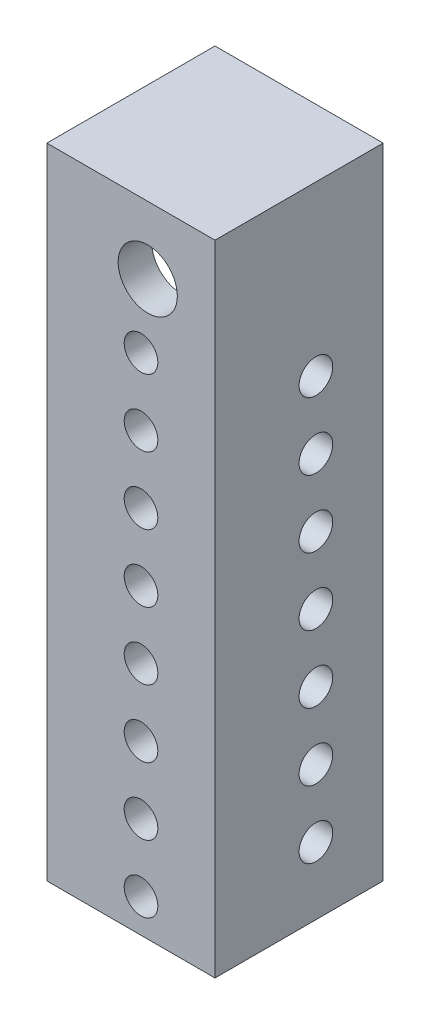
SolidWorks part; units mm, degrees
material "PET"
ref_plane "Front Plane" through (0, 0, 0) normal (0, 0, 1) x (1, 0, 0)
ref_plane "Top Plane" through (0, 0, 0) normal (0, 1, 0) x (1, 0, 0)
ref_plane "Right Plane" through (0, 0, 0) normal (1, 0, 0) x (0, 0, -1)
sketch "Sketch2" plane through (0, 0, 0) normal (0, 1, 0) x (1, 0, 0)
  line L1 (-41.3514, 38.3779) -> (22.1486, 38.3779)
  line L2 (-41.3514, 38.3779) -> (-41.3514, -25.1221)
  line L3 (-41.3514, -25.1221) -> (22.1486, -25.1221)
  line L4 (22.1486, 38.3779) -> (22.1486, -25.1221)
  dimension "D1" = 63.5
  dimension "D2" = 63.5
extrude "Boss-Extrude1" add sketch "Sketch2" along normal blind 241.3
ref_plane "Plane1" through (0, 116.078, 0) normal (0, 1, 0) x (1, 0, 0)
sketch "Sketch4" plane through (0, 116.078, 0) normal (0, 1, 0) x (1, 0, 0)
  line L0 (22.1486, -25.1221) -> (22.1486, 38.3779) construction
  line L1 (-41.3514, 38.3779) -> (9.4486, 38.3779)
  line L2 (-41.3514, 38.3779) -> (-41.3514, -12.4221)
  line L3 (-41.3514, -12.4221) -> (9.4486, -12.4221)
  line L4 (9.4486, 38.3779) -> (9.4486, -12.4221)
  line L5 (-41.3514, -25.1221) -> (22.1486, -25.1221) construction
  dimension "D1" = 12.7
  dimension "D2" = 12.7
extrude "Cut-Extrude1" cut sketch "Sketch4" along normal mid plane 190.5
sketch "Sketch5" plane through (0, 0, 25.1221) normal (0, 0, 1) x (1, 0, 0)
  line L1 (-41.3514, 0) -> (22.1486, 0) construction
  line L3 (-41.3514, 241.3) -> (-41.3514, 0) construction
  circle A4 centre (-5.7914, 12.7) radius 6.35
  circle A5 centre (-5.7914, 38.1) radius 6.35
  circle A6 centre (-5.7914, 63.5) radius 6.35
  circle A7 centre (-5.7914, 88.9) radius 6.35
  circle A8 centre (-5.7914, 114.3) radius 6.35
  circle A11 centre (-5.7914, 139.7) radius 6.35
  circle A12 centre (-5.7914, 165.1) radius 6.35
  circle A13 centre (-5.7914, 190.5) radius 6.35
  dimension "D1" = 35.56
  dimension "D4" = 12.7
  dimension "D3" = 12.7
  dimension "D2" = 8
extrude "Cut-Extrude2" cut sketch "Sketch5" against normal through all
sketch "Sketch6" plane through (22.1486, 0, 0) normal (1, 0, 0) x (0, 0, -1)
  line L0 (-25.1221, 0) -> (38.3779, 0) construction
  line L1 (38.3779, 241.3) -> (38.3779, 0) construction
  circle A4 centre (12.9779, 25.4) radius 6.35
  circle A5 centre (12.9779, 50.8) radius 6.35
  circle A6 centre (12.9779, 76.2) radius 6.35
  circle A7 centre (12.9779, 101.6) radius 6.35
  circle A8 centre (12.9779, 127) radius 6.35
  circle A9 centre (12.9779, 152.4) radius 6.35
  circle A10 centre (12.9779, 177.8) radius 6.35
  dimension "D1" = 25.4
  dimension "D4" = 12.7
  dimension "D2" = 25.4
  dimension "D3" = 7
extrude "Cut-Extrude3" cut sketch "Sketch6" against normal blind 12.7
sketch "Sketch7" plane through (0, 20.828, 0) normal (0, 1, 0) x (1, 0, 0)
  line L0 (22.1486, -25.1221) -> (22.1486, 38.3779) construction
  line L1 (-41.3514, 38.3779) -> (9.4486, 38.3779)
  line L2 (-41.3514, 38.3779) -> (-41.3514, -12.4221)
  line L3 (-41.3514, -12.4221) -> (-3.2514, -12.4221)
  line L4 (9.4486, 38.3779) -> (9.4486, 0.2779)
  line L5 (-41.3514, -25.1221) -> (22.1486, -25.1221) construction
  line L6 (9.4486, 0.2779) -> (9.4486, -12.4221)
  line L7 (9.4486, -12.4221) -> (-3.2514, -12.4221)
  dimension "D1" = 12.7
  dimension "D2" = 12.7
extrude "Cut-Extrude4" cut sketch "Sketch7" against normal through all
ref_plane "Plane2" through (0, 228.6, 0) normal (0, 1, 0) x (1, 0, 0)
sketch "Sketch42" plane through (0, 211.328, 0) normal (0, -1, 0) x (1, 0, 0)
  line L0 (-3.2514, 12.4221) -> (9.4486, 12.4221)
  line L1 (-41.3514, 12.4221) -> (-3.2514, 12.4221)
  line L2 (-41.3514, 12.4221) -> (-41.3514, -38.3779)
  line L3 (-41.3514, -38.3779) -> (9.4486, -38.3779)
  line L4 (9.4486, -0.2779) -> (9.4486, -38.3779)
  line L5 (9.4486, 12.4221) -> (9.4486, -0.2779)
extrude "Cut-Extrude8" cut sketch "Sketch42" against normal up to surface (17.272 mm away)
sketch "Sketch43" plane through (0, 228.6, 0) normal (0, 1, 0) x (1, 0, 0)
  line L0 (-41.3514, 38.3779) -> (-41.3514, -25.1221) construction
  line L1 (-10.8714, 33.5519) -> (-0.7114, 33.5519)
  line L2 (-10.8714, 33.5519) -> (-10.8714, 24.6619)
  line L3 (-10.8714, 24.6619) -> (-0.7114, 24.6619)
  line L4 (-0.7114, 33.5519) -> (-0.7114, 24.6619)
  line L5 (-10.8714, 16.7879) -> (-0.7114, 16.7879)
  line L6 (-10.8714, 16.7879) -> (-10.8714, 7.8979)
  line L7 (-10.8714, 7.8979) -> (-0.7114, 7.8979)
  line L8 (-0.7114, 16.7879) -> (-0.7114, 7.8979)
  line L9 (-41.3514, -25.1221) -> (22.1486, -25.1221) construction
  point P10 (0, 0)
  point P11 (11.8683, 18.5659)
  point P14 (0, 0)
  point P15 (0, 0)
  point P16 (0, 0)
  dimension "D1" = 33.02
  dimension "D2" = 7.874
  dimension "D3" = 8.89
  dimension "D4" = 10.16
  dimension "D6" = 30.48
extrude "Boss-Extrude4" add sketch "Sketch43" against normal blind 10.16
sketch "Sketch46" plane through (0, 0, -33.5519) normal (0, 0, -1) x (-1, 0, 0)
  line L0 (0.7114, 218.44) -> (10.8714, 218.44) construction
  line L1 (10.8714, 218.44) -> (10.8714, 228.6) construction
  circle A0 centre (5.7914, 223.52) radius 2.032
  dimension "D1" = 5.08
  dimension "D2" = 5.08
extrude "Cut-Extrude10" cut sketch "Sketch46" against normal up to surface (58.674 mm away) up to face at (0.5586, 190.5, 25.1221)
fillet "Fillet6" radius 3.81 4 edges at (-0.7114, 218.44, -12.3429) (-10.8714, 218.44, -12.3429) (-0.7114, 218.44, -29.1069) (-10.8714, 218.44, -29.1069)
sketch "Sketch47" plane through (0, 0, 0) normal (0, 1, 0) x (1, 0, 0)
  line L1 (-41.3514, -25.1221) -> (22.1486, -25.1221)
  line L2 (-41.3514, -25.1221) -> (-41.3514, 38.3779)
  line L3 (-41.3514, 38.3779) -> (22.1486, 38.3779)
  line L4 (22.1486, -25.1221) -> (22.1486, 38.3779)
sketch "Sketch48" plane through (0, 0, 25.1221) normal (0, 0, 1) x (1, 0, 0)
  line L0 (-41.3514, 241.3) -> (22.1486, 241.3) construction
  line L1 (-41.3514, 241.3) -> (-41.3514, 31.75) construction
  circle A0 centre (-3.2514, 215.9) radius 11.176
  dimension "D1" = 25.4
  dimension "D3" = 22.352
  dimension "D2" = 38.1
extrude "Cut-Extrude12" cut sketch "Sketch48" against normal blind 12.7
